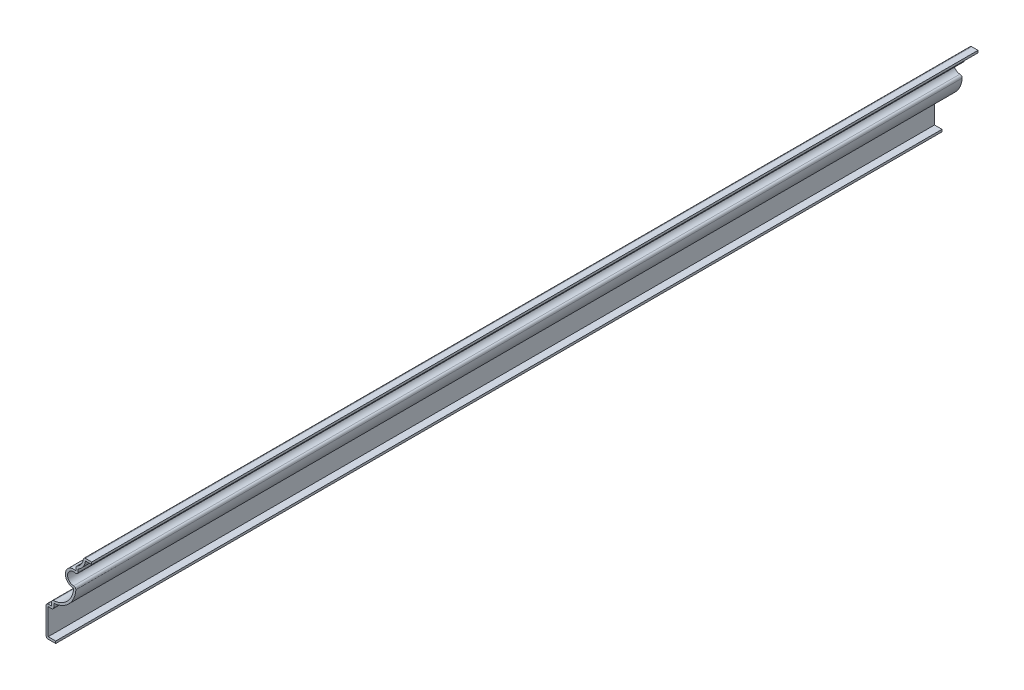
SolidWorks part; units mm, degrees
ref_plane "Front Plane" through (0, 0, 0) normal (0, 0, 1) x (1, 0, 0)
ref_plane "Top Plane" through (0, 0, 0) normal (0, 1, 0) x (1, 0, 0)
ref_plane "Right Plane" through (0, 0, 0) normal (1, 0, 0) x (0, 0, -1)
sketch "Sketch1" plane through (0, 0, 0) normal (0, 0, 1) x (1, 0, 0)
  line L0 (0, 0) -> (-5.5562, 0)
  line L1 (-5.5562, 0) -> (-5.5562, 17.4625)
  line L2 (-5.5562, 17.4625) -> (-2.3812, 17.4625)
  line L3 (-2.3812, 17.4625) -> (-2.3812, 20.6375)
  line L4 (11.5639, 41.8963) -> (11.5639, 44.2775)
  line L5 (15.875, 50.8) -> (20.6375, 50.8)
  line L6 (10.2939, 32.5437) -> (12.7662, 32.5437) construction
  arc A0 (-2.3812, 20.6375) -> (10.2939, 32.5437) centre (-2.3812, 33.3375) ccw
  arc A2 (11.5639, 41.8963) -> (10.2939, 32.5437) centre (10.2939, 37.3062) ccw
  arc A3 (11.5639, 44.2775) -> (15.875, 50.8) centre (8.9864, 50.6671) ccw
  dimension "D5" = 4.7625
  dimension "D6" = 12.7
  dimension "D13" = 6.8899
  dimension "D1" = 50.8
  dimension "D2" = 5.5562
  dimension "D3" = 17.4625
  dimension "D4" = 3.175
  dimension "D7" = 3.175
  dimension "D8" = 1.27
  dimension "D9" = 4.7625
  dimension "D10" = 26.1937
  dimension "D11" = 11.9062
  dimension "D12" = 2.3813
extrude "Extrude-Thin1" add sketch "Sketch1" against normal blind 508 thin contours L5 A3 L4 A2 A0 L3 L2 L1 L0
fillet "Fillet1" radius 1.27 8 edges at (15.875, 50.8, -254) (11.5639, 44.2775, -254) (12.8339, 39.7033, -254) (11.5703, 34.0553, -254) (-5.5562, 0, -254) (-1.1112, 16.1925, -254) (-2.3813, 20.6375, -254) (-5.5562, 17.4625, -254)
